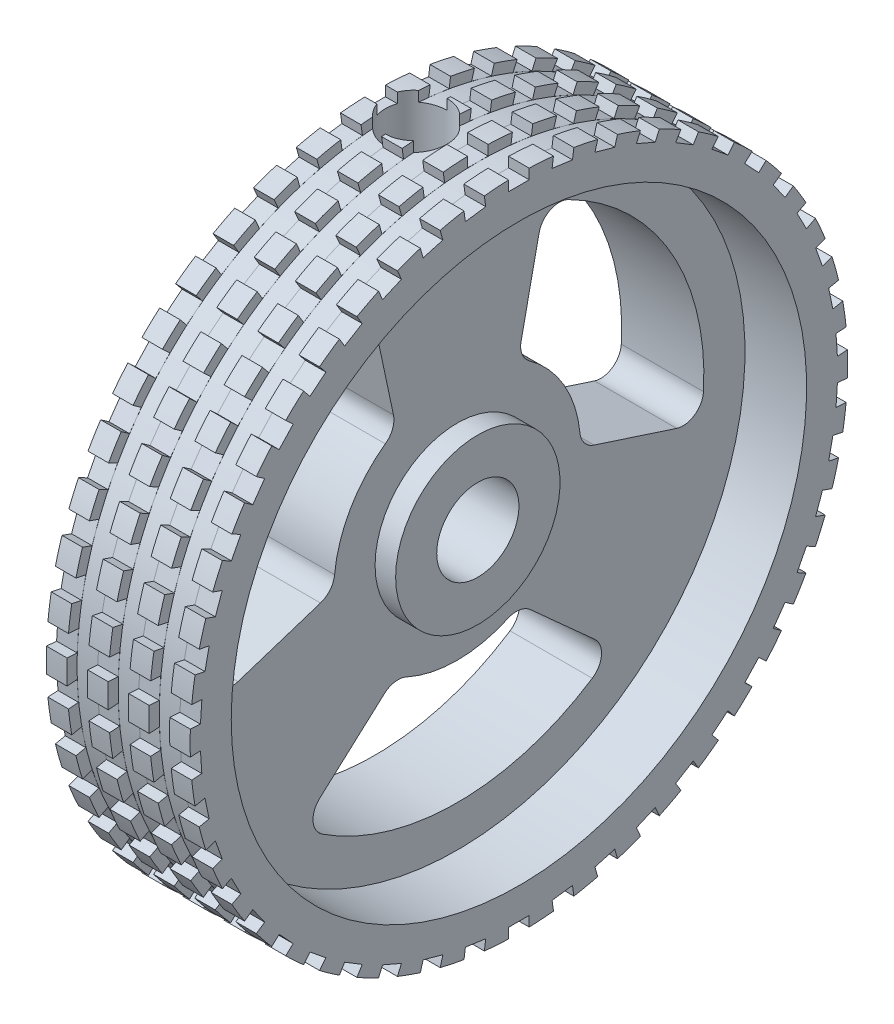
SolidWorks part; units mm, degrees
ref_plane "Front Plane" through (0, 0, 0) normal (0, 0, 1) x (1, 0, 0)
ref_plane "Top Plane" through (0, 0, 0) normal (0, 1, 0) x (1, 0, 0)
ref_plane "Right Plane" through (0, 0, 0) normal (1, 0, 0) x (0, 0, -1)
sketch "Sketch1" plane through (0, 0, 0) normal (0, 0, 1) x (1, 0, 0)
  line L0 (0, 2) -> (0, 16)
  line L1 (0, 16) -> (7, 16)
  line L2 (7, 16) -> (7, 14)
  line L3 (7, 14) -> (4, 14)
  line L4 (4, 14) -> (4, 4)
  line L5 (4, 4) -> (5, 4)
  line L6 (5, 4) -> (5, 2)
  line L7 (5, 2) -> (0, 2)
  line L8 (0, 0) -> (13.736, 0) construction
  dimension "D1" = 7
  dimension "D2" = 5
  dimension "D3" = 4
  dimension "D4" = 32
  dimension "D5" = 28
  dimension "D6" = 8
  dimension "D7" = 4
revolve "Revolve1" add sketch "Sketch1" angle 360 about L8
sketch "Sketch2" plane through (0, 0, 0) normal (0, 0, 1) x (1, 0, 0)
  line L0 (0, 0) -> (7, 0) construction
  line L1 (7, -16) -> (7, 16) construction
  line L2 (2, 0) -> (2.9, 0)
  line L3 (2.9, 0) -> (2.9, 11.5)
  line L4 (2.9, 11.5) -> (3.5, 11.5)
  line L5 (3.5, 11.5) -> (3.5, 16)
  line L6 (7, 16) -> (0, 16) construction
  line L7 (3.5, 16) -> (2, 16)
  line L8 (2, 16) -> (2, 0)
  line L9 (0, 16) -> (0, -16) construction
  line L10 (2, 0) -> (2, 18.3992) construction
  dimension "D1" = 2
  dimension "D2" = 4.5
  dimension "D3" = 1.8
revolve "Cut-Revolve1" cut sketch "Sketch2" angle 360 about L8
sketch "Sketch4" plane through (4, 0, 0) normal (1, 0, 0) x (0, 0, -1)
  line L0 (0, 0) -> (0, 19.9529) construction
  line L1 (0, 0) -> (-17.7269, 10.2346) construction
  line L2 (-4.2392, 11.2263) -> (-2.962, 5.2179)
  line L3 (-5.9998, -0.0437) -> (-11.8418, -1.9419)
  arc A0 (-2.962, 5.2179) -> (-5.9998, -0.0437) centre (0, 0) ccw
  arc A1 (-4.2392, 11.2263) -> (-11.8418, -1.9419) centre (0, 0) ccw
  dimension "D2" = 12
  dimension "D3" = 6
  dimension "D1" = 60
  dimension "D4" = 12
  dimension "D5" = 6.0084
extrude "Cut-Extrude2" cut sketch "Sketch4" against normal through all
fillet "Fillet2" radius 1 4 edges at (2, -0.0437, 5.9998) (2, 5.2179, 2.962) (2, -1.9419, 11.8418) (2, 11.2263, 4.2392)
pattern_circular "CirPattern2" count 3 over 360 about axis through (0, 0, 0) along (1, 0, 0) of "Fillet2", "Cut-Extrude2"
sketch "Sketch5" plane through (0, 0, 0) normal (0, 0, 1) x (1, 0, 0)
  line L0 (7, 16) -> (3.5, 16) construction
  line L1 (5, 16) -> (6, 16)
  line L2 (5, 16) -> (5, 15.5)
  line L3 (5, 15.5) -> (6, 15.5)
  line L4 (6, 16) -> (6, 15.5)
  line L5 (7, -16) -> (7, 16) construction
  line L6 (0, 0) -> (14.0489, 0) construction
  dimension "D1" = 1
  dimension "D2" = 0.5
  dimension "D3" = 1
revolve "Cut-Revolve2" cut sketch "Sketch5" angle 360 about L6
sketch "Sketch8" plane through (0, 0, 0) normal (-1, 0, 0) x (0, 0, 1)
  line L0 (0, 0) -> (0, 25.3502) construction
  line L2 (-0.5, 16) -> (0.5, 16)
  line L3 (-0.5, 16) -> (-0.5, 15.5)
  line L4 (-0.5, 15.5) -> (0.5, 15.5)
  line L5 (0.5, 16) -> (0.5, 15.5)
  circle A0 centre (0, 0) radius 16 construction
  dimension "D1" = 1
  dimension "D2" = 0.5
extrude "Cut-Extrude4" cut sketch "Sketch8" against normal blind 10
pattern_circular "CirPattern3" count 46 over 360 about axis through (0, 0, 0) along (1, 0, 0) of "Cut-Extrude4", "Cut-Revolve2"
pattern_linear "LPattern1" count 3 spacing 2 along (-1, 0, 0) of "Cut-Revolve2"
